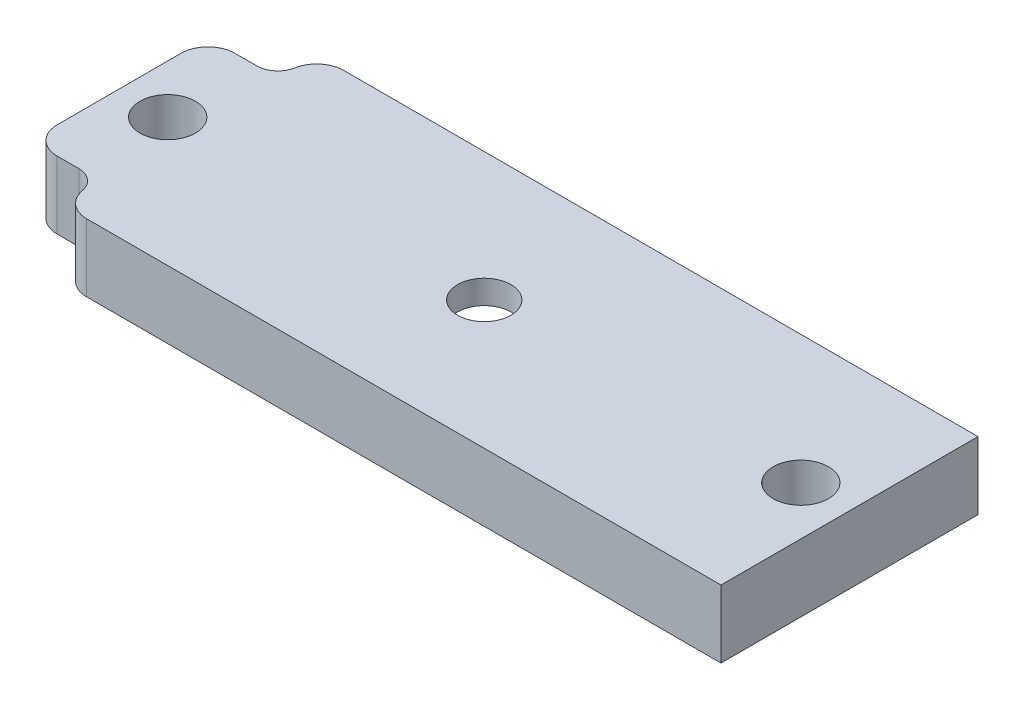
SolidWorks part; units mm, degrees
ref_plane "Front Plane" through (0, 0, 0) normal (0, 0, 1) x (1, 0, 0)
ref_plane "Top Plane" through (0, 0, 0) normal (0, 1, 0) x (1, 0, 0)
ref_plane "Right Plane" through (0, 0, 0) normal (1, 0, 0) x (0, 0, -1)
sketch "Sketch2" plane through (0, 0, 0) normal (0, 1, 0) x (1, 0, 0)
  line L1 (0, 0) -> (68.58, 0)
  line L2 (0, 0) -> (0, 24.13)
  line L3 (0, 24.13) -> (68.58, 24.13)
  line L4 (68.58, 0) -> (68.58, 24.13)
  circle A0 centre (4.57, 12.065) radius 2.6
  circle A1 centre (64.01, 12.065) radius 2.6
  point P10 (68.58, 12.065)
  dimension "D4" = 5.2
  dimension "D1" = 68.58
  dimension "D2" = 24.13
  dimension "D3" = 4.57
  dimension "D5" = 4.57
extrude "Boss-Extrude1" add sketch "Sketch2" along normal blind 6.35
sketch "Sketch3" plane through (0, 6.35, 0) normal (0, 1, 0) x (1, 0, 0)
  line L0 (6.57, 22.415) -> (6.57, 24.13)
  line L2 (4.57, 20.415) -> (0, 20.415)
  line L3 (0, 24.13) -> (0, 0) construction
  line L4 (68.58, 24.13) -> (0, 24.13) construction
  line L5 (4.57, 12.065) -> (64.01, 12.065) construction
  line L6 (34.29, 24.13) -> (34.29, 0) construction
  line L7 (0, 0) -> (68.58, 0) construction
  line L8 (6.57, 1.715) -> (6.57, 0)
  line L9 (4.57, 3.715) -> (0, 3.715)
  arc A0 (4.57, 20.415) -> (6.57, 22.415) centre (4.57, 22.415) ccw
  circle A1 centre (4.57, 12.065) radius 2.6 construction
  circle A2 centre (4.57, 12.065) radius 2.6
  arc A3 (4.57, 3.715) -> (6.57, 1.715) centre (4.57, 1.715) cw
  line M1 (0, 0) -> (68.58, 0)
  line M5 (68.58, 24.13) -> (0, 24.13)
  line M7 (0, 24.13) -> (0, 0)
  dimension "D1" = 10.35
  dimension "D2" = 4
extrude "Cut-Extrude1" cut sketch "Sketch3" against normal through all contours A3 L9 L8 M7 M1 | L2 A0 L0 M5 M7
fillet "Fillet3" radius 2.54 4 edges at (6.57, 3.175, 0) (0, 3.175, -3.715) (0, 3.175, -20.415) (6.57, 3.175, -24.13)
sketch "Sketch4" plane through (0, 6.35, 0) normal (0, 1, 0) x (1, 0, 0)
  line L0 (4.57, 12.065) -> (64.01, 12.065) construction
  circle A0 centre (34.29, 12.065) radius 2.5
  circle A1 centre (4.57, 12.065) radius 2.6 construction
  circle A2 centre (64.01, 12.065) radius 2.6 construction
  circle A3 centre (64.01, 12.065) radius 2.6 construction
  circle A4 centre (4.57, 12.065) radius 2.6 construction
  point P8 (34.29, 12.065)
  dimension "D1" = 5
extrude "Cut-Extrude2" cut sketch "Sketch4" against normal through all
ref_plane "Plane2" through (34.29, 0, 0) normal (1, 0, 0) x (0, 0, -1)
sketch "Sketch8" plane through (34.29, 0, 0) normal (1, 0, 0) x (0, 0, -1)
  line L0 (0, 6.35) -> (24.13, 6.35) construction
  line L1 (0, 6.35) -> (24.13, 6.35) construction
  line L2 (12.065, 6.35) -> (12.065, 0) construction
  line L3 (0, 0) -> (24.13, 0) construction
  line L4 (22.13, 0) -> (24.13, 0) construction
  line L5 (12.065, 4.35) -> (12.065, 0)
  line L6 (0, 0) -> (24.13, 0)
  circle A0 centre (12.065, -9.4692) radius 13.8192
  point P8 (12.065, 4.35)
  dimension "D1" = 2
  dimension "D2" = 2
revolve "Cut-Revolve6" cut sketch "Sketch8" angle 360 about L2
